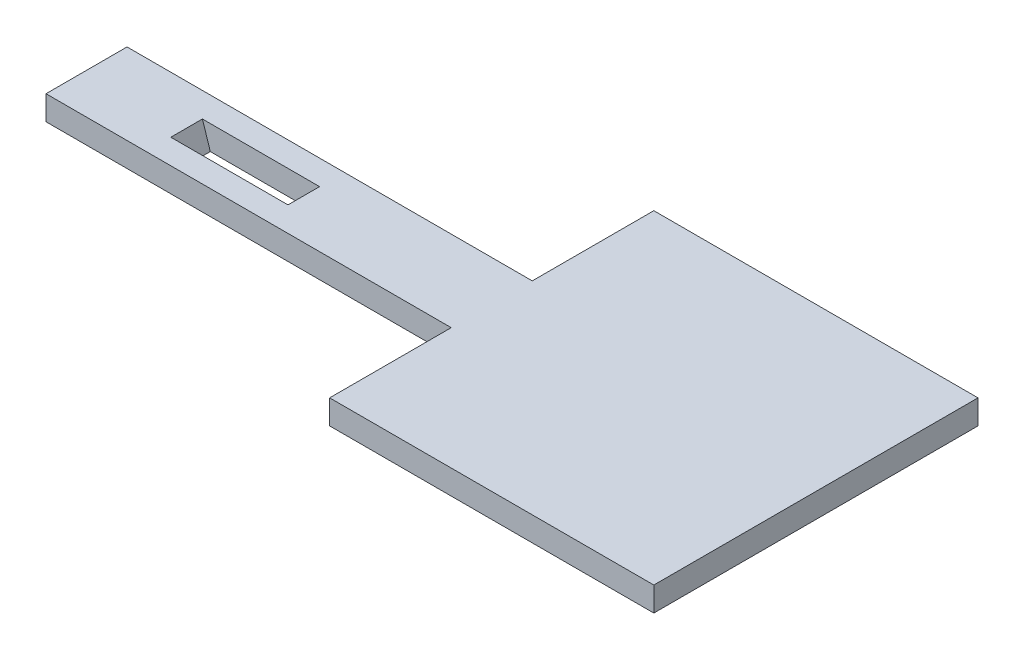
SolidWorks part; units mm, degrees
ref_plane "前基準面" through (0, 0, 0) normal (0, 0, 1) x (1, 0, 0)
ref_plane "上基準面" through (0, 0, 0) normal (0, 1, 0) x (1, 0, 0)
ref_plane "右基準面" through (0, 0, 0) normal (1, 0, 0) x (0, 0, -1)
sketch "草圖1" plane through (0, 0, 0) normal (0, 1, 0) x (1, 0, 0)
  line L0 (22, 5.3158) -> (22, 20.3158)
  line L1 (-28, 5.3158) -> (22, 5.3158)
  line L2 (-28, 5.3158) -> (-28, -4.6842)
  line L3 (-28, -4.6842) -> (22, -4.6842)
  line L4 (0, 0.3158) -> (-28, 0.3158) construction
  line L5 (22, 20.3158) -> (62, 20.3158)
  line L6 (62, 20.3158) -> (62, -19.6842)
  line L7 (62, -19.6842) -> (22, -19.6842)
  line L8 (22, -19.6842) -> (22, -4.6842)
  dimension "D1" = 10
  dimension "D2" = 40
  dimension "D3" = 40
  dimension "D4" = 90
extrude "填料-伸長1" add sketch "草圖1" along normal blind 3
ref_plane "平面1" through (5.9205, -18.2213, 0) normal (0.309, -0.9511, 0) x (0, 0, -1)
sketch "草圖3" plane through (0, 0, 4.6842) normal (0, 0, 1) x (1, 0, 0)
  line L0 (-28, 0) -> (22, 0) construction
  line L1 (-15.6498, 3) -> (-1.1922, 3)
  line L2 (-1.2466, 3.1674) -> (-1.9494, 5.3305) construction
  line L3 (-0.2174, 0) -> (-1.1922, 3)
  line L4 (-14.675, 0) -> (-0.2174, 0)
  line L5 (-28, 3) -> (22, 3) construction
  line L6 (-28, 3) -> (-28, 0) construction
  line L7 (-14.675, 0) -> (-15.6498, 3)
  line L8 (-15.0028, -25.0197) -> (26.8437, -11.423) construction
  dimension "D1" = 13.325
  dimension "D2" = 13.75
extrude "除料-伸長1" cut sketch "草圖3" against normal mid plane 3.9 from offset 5
